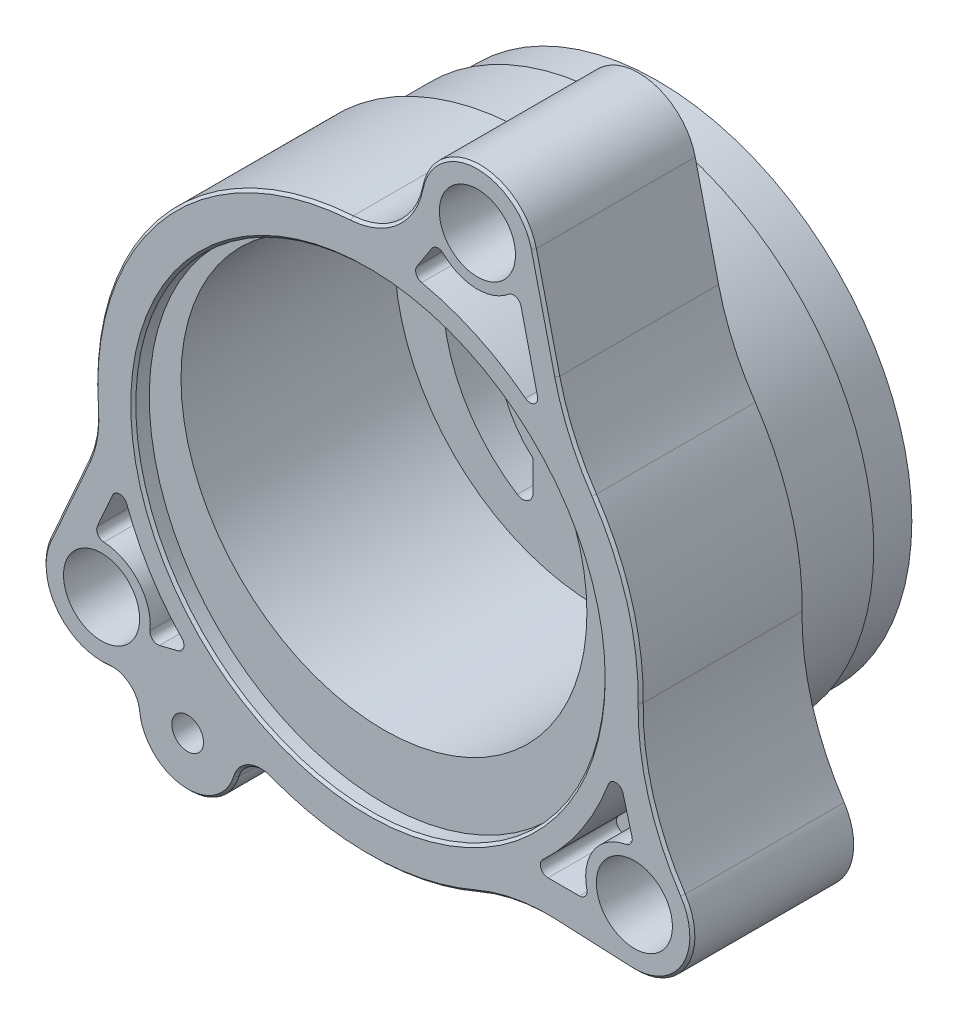
SolidWorks part; units mm, degrees
material "7075-T6 (SN)"
ref_plane "Plane1" through (0, 0, 0) normal (0, 0, 1) x (1, 0, 0)
ref_plane "Plane2" through (0, 0, 0) normal (0, 1, 0) x (-1, 0, 0)
ref_plane "Plane3" through (0, 0, 0) normal (1, 0, 0) x (0, 0, -1)
sketch "Sketch1" plane through (0, 0, 0) normal (0, 0, 1) x (1, 0, 0)
  line L0 (-26.67, -18.1463) -> (26.67, -18.1463) construction
  line L1 (0, 0) -> (-26.67, -18.1463) construction
  line L2 (0, 0) -> (26.67, -18.1463) construction
  line L3 (10.9563, 32.2244) -> (0, 0) construction
  line L4 (16.6043, 33.5606) -> (18.9435, 23.6736)
  line L6 (18.789, -23.5906) -> (26.4008, -23.944)
  line L11 (-28.0689, -6.9945) -> (-31.9746, -15.7912)
  line L12 (-18.0518, -25.6544) -> (0, 0) construction
  arc A1 (-31.9746, -15.7912) -> (-25.9484, -23.9052) centre (-26.67, -18.1463) ccw
  arc A3 (16.6043, 33.5606) -> (5.2649, 33.3618) centre (10.9563, 32.2244) ccw
  arc A4 (27.3007, -0.4835) -> (22.6196, 15.2943) centre (0, 0) ccw
  arc A5 (31.511, -14.9447) -> (27.3007, -0.4835) centre (52.6967, -0.9332) cw
  arc A6 (5.2649, 33.3618) -> (-1.7257, 27.2504) centre (-2.2073, 34.8552) cw
  arc A7 (-1.7257, 27.2504) -> (-27.2247, -2.0929) centre (0, 0) ccw
  arc A9 (26.4008, -23.944) -> (31.511, -14.9447) centre (26.67, -18.1463) ccw
  arc A10 (-9.8371, -25.4714) -> (10.8798, -25.0438) centre (0, 0) ccw
  arc A12 (-27.2247, -2.0929) -> (-28.0689, -6.9945) centre (-37.3548, -2.8716) cw
  arc A13 (22.6196, 15.2943) -> (18.9435, 23.6736) centre (43.6611, 29.5216) cw
  arc A14 (18.789, -23.5906) -> (10.8798, -25.0438) centre (17.9643, -41.3514) ccw
  arc A15 (-23.1057, -26.1685) -> (-13.1854, -27.112) centre (-18.0518, -25.6544) ccw
  arc A16 (-9.8371, -25.4714) -> (-13.1854, -27.112) centre (-10.7522, -27.8409) ccw
  arc A17 (-23.1057, -26.1685) -> (-25.9484, -23.9052) centre (-25.6326, -26.4255) ccw
  dimension "D1" = 54.61
  dimension "D2" = 53.34
  dimension "D3" = 11.6078
  dimension "D4" = 32.258
  dimension "D7" = 25.4
  dimension "D8" = 10.16
  dimension "D9" = 7.62
  dimension "D10" = 25.4
  dimension "D11" = 17.78
  dimension "D14" = 2.54
  dimension "D15" = 2.54
  dimension "D16" = 5.08
  dimension "D5" = 34.036
  dimension "D6" = 105.453
  dimension "D12" = 10.16
  dimension "D13" = 7.62
  dimension "D17" = 31.369
  dimension "D18" = 11.43
  dimension "D19" = 9.6247
extrude "Base" add sketch "Sketch1" along normal blind 16.1544
sketch "Sketch2" plane through (0, 0, 0) normal (0, 0, -1) x (-1, 0, 0)
  circle A0 centre (0, 0) radius 25.9715
  arc A1 (27.2247, -2.0929) -> (1.7257, 27.2504) centre (0, 0) ccw construction
  dimension "D1" = 51.943
extrude "Boss I" add sketch "Sketch2" along normal blind 8.509
sketch "Sketch3" plane through (0, 0, -8.509) normal (0, 0, -1) x (-1, 0, 0)
  circle A0 centre (0, 0) radius 25.4635
  circle A1 centre (0, 0) radius 25.9715 construction
  dimension "D1" = 50.927
extrude "Boss II" add sketch "Sketch3" along normal blind 4.318
sketch "Sketch4" plane through (0, 0, 16.1544) normal (0, 0, 1) x (1, 0, 0)
  circle A0 centre (0, 0) radius 23.495
  arc A1 (27.3007, -0.4835) -> (22.6196, 15.2943) centre (0, 0) ccw construction
  dimension "D1" = 46.99
extrude "Top Seal Cut" cut sketch "Sketch4" against normal blind 1.6002
sketch "Sketch5" plane through (0, 0, 14.5542) normal (0, 0, 1) x (1, 0, 0)
  line L0 (0, -50) -> (0, 50) construction
  circle A0 centre (0, 3.175) radius 20.32
  circle A1 centre (0, 0) radius 23.495 construction
  dimension "D1" = 40.64
extrude "Eccentric" cut sketch "Sketch5" against normal blind 21.3868
sketch "Sketch6" plane through (0, 0, -12.827) normal (0, 0, -1) x (-1, 0, 0)
  line L0 (-1.27, 19.8406) -> (-1.27, 10.5065)
  line L1 (1.27, 19.8406) -> (1.27, 10.5065)
  line L2 (-1.27, -10.5065) -> (-1.27, -19.8406)
  line L3 (1.27, -10.5065) -> (1.27, -19.8406)
  circle A0 centre (0, 0) radius 23.9395
  arc A1 (-2.7013, 21.1003) -> (-2.7013, -21.1003) centre (0, 0) ccw
  arc A2 (2.9441, -8.1187) -> (2.9441, 8.1187) centre (0, 0) ccw
  circle A3 centre (0, 0) radius 25.4635 construction
  arc A4 (2.7013, -21.1003) -> (2.7013, 21.1003) centre (0, 0) ccw
  arc A5 (-2.9441, 8.1187) -> (-2.9441, -8.1187) centre (0, 0) ccw
  arc A8 (-1.27, 19.8406) -> (-2.7013, 21.1003) centre (-2.54, 19.8406) ccw
  arc A9 (2.7013, 21.1003) -> (1.27, 19.8406) centre (2.54, 19.8406) ccw
  arc A10 (-2.7013, -21.1003) -> (-1.27, -19.8406) centre (-2.54, -19.8406) ccw
  arc A11 (2.7013, -21.1003) -> (1.27, -19.8406) centre (2.54, -19.8406) cw
  arc A12 (-1.27, -10.5065) -> (-2.9441, -8.1187) centre (-3.81, -10.5065) ccw
  arc A13 (-1.27, 10.5065) -> (-2.9441, 8.1187) centre (-3.81, 10.5065) cw
  arc A14 (2.9441, -8.1187) -> (1.27, -10.5065) centre (3.81, -10.5065) ccw
  arc A15 (2.9441, 8.1187) -> (1.27, 10.5065) centre (3.81, 10.5065) cw
  dimension "D1" = 42.545
  dimension "D2" = 47.879
  dimension "D3" = 17.272
  dimension "D8" = 1.27
  dimension "D9" = 2.54
  dimension "D4" = 2.54
extrude "Bottom Seal Cut" cut sketch "Sketch6" against normal blind 1.27
sketch "Sketch7" plane through (0, 0, -12.827) normal (0, 0, -1) x (-1, 0, 0)
  line L0 (6.477, 7.4952) -> (6.477, 14.3943)
  line L1 (6.477, -7.4952) -> (6.477, -10.5715)
  line L3 (1.27, 19.8406) -> (1.27, 10.5065) construction
  arc A1 (3.377, -9.3126) -> (3.377, 9.3126) centre (0, 0) ccw
  arc A2 (6.477, -7.4952) -> (6.477, 7.4952) centre (0, 0) ccw
  arc A3 (8.4636, 15.4428) -> (8.0395, -11.428) centre (-0.6227, 2.1475) cw
  arc A4 (8.4636, 15.4428) -> (6.477, 14.3943) centre (7.747, 14.3943) ccw
  arc A5 (8.0395, -11.428) -> (6.477, -10.5715) centre (7.493, -10.5715) cw
  dimension "D5" = 16.1036
  dimension "D2" = 1.27
  dimension "D3" = 1.016
  dimension "D4" = 6.8991
  dimension "D6" = 5.207
  dimension "D7" = 3.0763
  dimension "D1" = 1.27
extrude "Intake Port" cut sketch "Sketch7" against normal through all
sketch "Sketch8" plane through (0, 0, -12.827) normal (0, 0, -1) x (-1, 0, 0)
  line L0 (-9.525, 2.7209) -> (-9.525, 9.0709)
  line L1 (-3.4544, -9.2842) -> (-3.4544, -11.0622)
  line L2 (-1.27, -10.5065) -> (-1.27, -19.8406) construction
  line L3 (-1.27, 19.8406) -> (-1.27, 10.5065) construction
  arc A0 (-9.525, 2.7209) -> (-3.4544, -9.2842) centre (0, 0) ccw
  arc A1 (6.477, -7.4952) -> (6.477, 7.4952) centre (0, 0) ccw construction
  arc A2 (-9.525, 9.0709) -> (-13.778, 10.0633) centre (-11.7673, 9.0709) ccw
  arc A3 (-13.778, 10.0633) -> (-5.1925, -12.2428) centre (0.7993, 2.8687) ccw
  arc A4 (-3.4544, -11.0622) -> (-5.1925, -12.2428) centre (-4.7244, -11.0622) cw
  dimension "D3" = 16.256
  dimension "D4" = 2.2423
  dimension "D5" = 1.27
  dimension "D1" = 2.1844
  dimension "D2" = 8.255
  dimension "D6" = 6.35
  dimension "D7" = 1.778
extrude "Exhaust Port" cut sketch "Sketch8" against normal through all
sketch "Sketch9" plane through (0, 0, -12.827) normal (0, 0, -1) x (-1, 0, 0)
  line L0 (3.1496, -11.2999) -> (3.1496, -18.5143)
  line L1 (1.27, -10.5065) -> (1.27, -19.8406) construction
  line L2 (15.7862, -6.5664) -> (17.4463, -6.5664)
  arc A0 (4.453, -11.1723) -> (9.1599, -13.1838) centre (7.493, -10.5715) ccw
  arc A1 (9.1599, -13.1838) -> (15.1263, -6.9473) centre (-0.6227, 2.1475) ccw
  arc A2 (4.0691, -19.2598) -> (18.1489, -7.6235) centre (0, 0) ccw
  arc A3 (2.7013, -21.1003) -> (2.7013, 21.1003) centre (0, 0) ccw construction
  arc A4 (8.0395, -11.428) -> (8.4636, 15.4428) centre (-0.6227, 2.1475) ccw construction
  arc A5 (6.477, -10.5715) -> (8.0395, -11.428) centre (7.493, -10.5715) ccw construction
  arc A6 (4.0691, -19.2598) -> (3.1496, -18.5143) centre (3.9116, -18.5143) cw
  arc A7 (15.7862, -6.5664) -> (15.1263, -6.9473) centre (15.7862, -7.3284) ccw
  arc A8 (18.1489, -7.6235) -> (17.4463, -6.5664) centre (17.4463, -7.3284) ccw
  arc A9 (3.1496, -11.2999) -> (4.453, -11.1723) centre (3.8075, -11.2999) cw
  dimension "D1" = 19.685
  dimension "D3" = 18.1864
  dimension "D4" = 0.762
  dimension "D7" = 0.6579
  dimension "D2" = 1.8796
extrude "Pocket 1" cut sketch "Sketch9" against normal blind 2.794
sketch "Sketch10" plane through (0, 0, -12.827) normal (0, 0, -1) x (-1, 0, 0)
  line L0 (-3.1496, -16.3751) -> (-3.1496, -18.5143)
  line L1 (-18.5003, -3.2154) -> (-17.7923, -3.2154)
  line L3 (-1.27, -10.5065) -> (-1.27, -19.8406) construction
  arc A0 (-17.0772, -3.7141) -> (-3.7304, -15.6349) centre (0.7993, 2.8687) ccw
  arc A1 (-19.2452, -4.1376) -> (-4.0691, -19.2598) centre (0, 0) ccw
  arc A2 (-13.778, 10.0633) -> (-5.1925, -12.2428) centre (0.7993, 2.8687) ccw construction
  arc A3 (-2.7013, 21.1003) -> (-2.7013, -21.1003) centre (0, 0) ccw construction
  arc A4 (-3.1496, -18.5143) -> (-4.0691, -19.2598) centre (-3.9116, -18.5143) cw
  arc A5 (-3.1496, -16.3751) -> (-3.7304, -15.6349) centre (-3.9116, -16.3751) ccw
  arc A6 (-18.5003, -3.2154) -> (-19.2452, -4.1376) centre (-18.5003, -3.9774) ccw
  arc A7 (-17.0772, -3.7141) -> (-17.7923, -3.2154) centre (-17.7923, -3.9774) ccw
  dimension "D1" = 19.685
  dimension "D2" = 19.05
  dimension "D4" = 0.762
  dimension "D3" = 1.8796
extrude "Pocket 2" cut sketch "Sketch10" against normal blind 2.794
sketch "Sketch11" plane through (0, 0, -12.827) normal (0, 0, -1) x (-1, 0, 0)
  line L0 (-3.1496, 17.8908) -> (-3.1496, 9.7129)
  line L2 (-1.27, 19.8406) -> (-1.27, 10.5065) construction
  arc A0 (-11.4035, 15.2915) -> (-4.0744, 18.6352) centre (0, 0) cw
  arc A1 (-11.0581, 13.9267) -> (-6.8602, 9.1153) centre (-11.7673, 9.0709) cw
  arc A2 (-5.6747, 8.4887) -> (-3.1496, 9.7129) centre (0, 0) cw
  arc A3 (-2.9441, 8.1187) -> (-2.9441, -8.1187) centre (0, 0) ccw construction
  arc A4 (-2.7013, 21.1003) -> (-2.7013, -21.1003) centre (0, 0) ccw construction
  arc A5 (-9.525, 9.0709) -> (-13.778, 10.0633) centre (-11.7673, 9.0709) ccw construction
  arc A6 (-11.4035, 15.2915) -> (-11.0581, 13.9267) centre (-10.948, 14.6807) ccw
  arc A7 (-5.6747, 8.4887) -> (-6.8602, 9.1153) centre (-6.0982, 9.1222) cw
  arc A8 (-3.1496, 17.8908) -> (-4.0744, 18.6352) centre (-3.9116, 17.8908) ccw
  dimension "D2" = 19.0754
  dimension "D3" = 10.2108
  dimension "D4" = 4.9073
  dimension "D5" = 0.762
  dimension "D1" = 1.8796
extrude "Pocket 3" cut sketch "Sketch11" against normal blind 2.794
sketch "Sketch12" plane through (0, 0, -11.557) normal (0, 0, -1) x (-1, 0, 0)
  circle A0 centre (0, 0) radius 6.1595
  arc A1 (2.9441, -8.1187) -> (2.9441, 8.1187) centre (0, 0) ccw construction
  dimension "D1" = 12.319
extrude "Shaft Boss" add sketch "Sketch12" along normal blind 2.794
sketch "Sketch13" plane through (0, 0, -14.351) normal (0, 0, -1) x (-1, 0, 0)
  circle A1 centre (0, 0) radius 4.8895
  circle A2 centre (0, 0) radius 4.8895
  dimension "D1" = 1.27
extrude "Shaft Race" cut sketch "Sketch13" against normal through all
fillet "Fillet1" radius 0.127 54 edges at (-9.906, 0, -12.827) (-6.477, 10.9447, -12.827) (-15.4789, 1.8934, -12.827) (-7.0046, -11.4624, -12.827) (-6.477, -9.0333, -12.827) (-7.1542, 15.5174, -12.827) (8.8401, -4.4702, -12.827) (3.4544, -10.1732, -12.827) (4.0108, -12.1127, -12.827) (9.525, 5.8959, -12.827) (11.2578, 11.2545, -12.827) (14.3718, -2.9706, -12.827) (-3.7435, -10.6451, -12.827) (-6.2753, -13.421, -12.827) (-12.5184, -10.4246, -12.827) (-16.6163, -6.5664, -12.827) (-3.4317, -19.1062, -12.827) (-3.1496, -14.9071, -12.827) (-12.5404, -15.1736, -12.827) (-18.081, -6.9066, -12.827) (-15.4052, -6.6685, -12.827) (3.4317, -19.1062, -12.827) (18.1463, -3.2154, -12.827) (11.8907, -11.3393, -12.827) (3.1496, -17.4447, -12.827) (3.3121, -15.9047, -12.827) (17.3564, -3.3524, -12.827) (19.093, -3.4986, -12.827) (13.8946, -13.9441, -12.827) (6.4543, 8.4485, -12.827) (7.9175, 17.3547, -12.827) (3.1496, 13.8018, -12.827) (4.4544, 9.188, -12.827) (3.4338, 18.4844, -12.827) (11.6867, 14.4937, -12.827) (8.0696, 12.2971, -12.827) (-6.1595, 0, -14.351) (-4.8895, 0, -14.351) (-1.7009, -20.7939, -12.827) (-8.636, 0, -12.827) (-1.7302, 9.0484, -12.827) (1.27, 15.1735, -12.827) (1.7302, 9.0484, -12.827) (8.636, 0, -12.827) (1.27, -15.1735, -12.827) (1.7009, 20.7939, -12.827) (1.7302, -9.0484, -12.827) (1.7009, -20.7939, -12.827) (21.2725, 0, -12.827) (-1.7009, 20.7939, -12.827) (-21.2725, 0, -12.827) (-1.27, -15.1735, -12.827) (-1.7302, -9.0484, -12.827) (-1.27, 15.1735, -12.827)
sketch "Sketch14" plane through (0, 0, 16.1544) normal (0, 0, 1) x (1, 0, 0)
  circle A0 centre (10.9563, 32.2244) radius 3.81
  circle A1 centre (-26.67, -18.1463) radius 3.81
  circle A2 centre (26.67, -18.1463) radius 3.81
  arc A3 (16.6043, 33.5606) -> (5.2649, 33.3618) centre (10.9563, 32.2244) ccw construction
  arc A4 (26.4008, -23.944) -> (31.511, -14.9447) centre (26.67, -18.1463) ccw construction
  arc A5 (-31.9746, -15.7912) -> (-25.9484, -23.9052) centre (-26.67, -18.1463) ccw construction
  dimension "D1" = 7.62
extrude "Mounting Holes" cut sketch "Sketch14" against normal through all draft 3
chamfer "Chamfer1" distance 0.254 angle 45 18 edges at (-20.6104, 17.9102, 16.1544) (-27.3422, -4.5962, 16.1544) (-30.0217, -11.3928, 16.1544) (-31.3294, -21.6068, 16.1544) (-24.0506, -24.4384, 16.1544) (-18.5328, -30.7116, 16.1544) (-11.8698, -25.56, 16.1544) (0.5635, -27.2992, 16.1544) (14.7512, -23.8642, 16.1544) (22.5949, -23.7673, 16.1544) (10.8545, 38.0274, 16.1544) (31.717, -21.0122, 16.1544) (28.3093, -8.0333, 16.1544) (26.1772, 7.7665, 16.1544) (20.4011, 19.3171, 16.1544) (17.7739, 28.6171, 16.1544) (23.495, 0, 16.1544) (2.808, 29.1183, 16.1544)
sketch "Sketch15" plane through (0, 0, 16.1544) normal (0, 0, 1) x (1, 0, 0)
  circle A0 centre (-18.0518, -25.6544) radius 1.5875
  arc A1 (-22.853, -26.1428) -> (-13.4287, -27.0392) centre (-18.0518, -25.6544) ccw construction
  dimension "D1" = 3.175
extrude "Screw Hole" cut sketch "Sketch15" against normal through all
sketch "Sketch16" plane through (0, 0, 0) normal (0, 0, -1) x (-1, 0, 0)
  circle A0 centre (18.0518, -25.6544) radius 3.302
  arc A1 (13.1854, -27.112) -> (23.1057, -26.1685) centre (18.0518, -25.6544) ccw construction
  dimension "D1" = 6.604
extrude "Screw C-Bore" cut sketch "Sketch16" against normal blind 13.462
sketch "Sketch17" plane through (0, 0, 16.1544) normal (0, 0, 1) x (1, 0, 0)
  line L3 (4.8919, 26.2974) -> (6.3855, 28.5974)
  line L4 (15.3178, 28.0764) -> (16.9729, 21.0808)
  line L5 (18.6963, 23.6151) -> (16.3571, 33.5022) construction
  line L6 (-25.5606, -8.7608) -> (-27.0899, -12.2051)
  line L7 (-20.8741, -19.4476) -> (-18.9949, -18.9769)
  line L8 (18.0221, -20.1449) -> (21.1684, -20.1449)
  line L9 (25.5319, -9.0553) -> (26.4334, -12.3933)
  line L10 (-27.8368, -7.0976) -> (-31.7424, -15.8942) construction
  arc A16 (5.3717, 25.1372) -> (15.764, 20.3035) centre (0, 0) cw
  arc A17 (7.5559, 28.7286) -> (14.0871, 28.4852) centre (10.9563, 32.2244) ccw
  circle A18 centre (0, 0) radius 23.749 construction
  circle A19 centre (10.9563, 32.2244) radius 3.81 construction
  arc A20 (16.9729, 21.0808) -> (15.764, 20.3035) centre (16.2314, 20.9054) cw
  arc A21 (15.3178, 28.0764) -> (14.0871, 28.4852) centre (14.5762, 27.9009) ccw
  arc A22 (6.3855, 28.5974) -> (7.5559, 28.7286) centre (7.0245, 28.1824) cw
  arc A23 (5.3717, 25.1372) -> (4.8919, 26.2974) centre (5.531, 25.8824) cw
  arc A24 (24.0824, -8.9876) -> (17.5032, -18.8248) centre (0, 0) cw
  arc A25 (-24.1483, -8.8089) -> (-18.6279, -17.7127) centre (0, 0) ccw
  arc A26 (-26.4308, -13.2754) -> (-21.8175, -18.6325) centre (-26.67, -18.1463) cw
  arc A27 (25.8291, -13.3426) -> (21.9119, -19.2158) centre (26.67, -18.1463) ccw
  circle A28 centre (26.67, -18.1463) radius 3.81 construction
  circle A29 centre (-26.67, -18.1463) radius 3.81 construction
  arc A30 (-24.1483, -8.8089) -> (-25.5606, -8.7608) centre (-24.8642, -9.07) ccw
  arc A31 (-26.4308, -13.2754) -> (-27.0899, -12.2051) centre (-26.3934, -12.5143) cw
  arc A32 (-20.8741, -19.4476) -> (-21.8175, -18.6325) centre (-21.0593, -18.7085) cw
  arc A33 (-18.6279, -17.7127) -> (-18.9949, -18.9769) centre (-19.1801, -18.2378) cw
  arc A34 (21.9119, -19.2158) -> (21.1684, -20.1449) centre (21.1684, -19.3829) cw
  arc A35 (26.4334, -12.3933) -> (25.8291, -13.3426) centre (25.6977, -12.592) cw
  arc A36 (25.5319, -9.0553) -> (24.0824, -8.9876) centre (24.7963, -9.254) ccw
  arc A37 (18.0221, -20.1449) -> (17.5032, -18.8248) centre (18.0221, -19.3829) cw
  dimension "D1" = 4.8768
  dimension "D2" = 25.7048
  dimension "D4" = 0.762
  dimension "D5" = 0.762
  dimension "D6" = 0.762
  dimension "D7" = 0.762
  dimension "D8" = 0.762
  dimension "D9" = 0.762
  dimension "D10" = 0.762
  dimension "D11" = 0.762
  dimension "D12" = 0.762
  dimension "D13" = 0.762
  dimension "D14" = 0.762
  dimension "D15" = 0.762
  dimension "D3" = 2.2606
extrude "Casting Cuts" cut sketch "Sketch17" against normal blind 7.62
